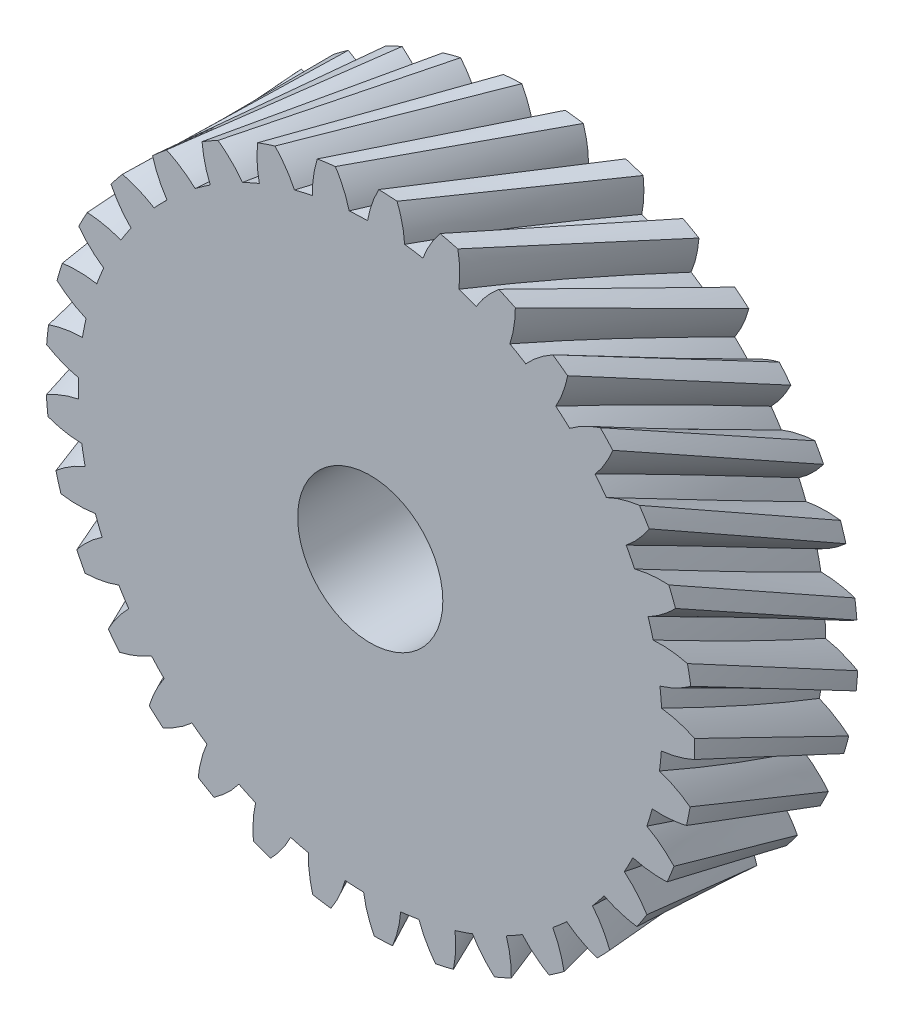
SolidWorks part; units mm, degrees
ref_plane "Front Plane" through (0, 0, 0) normal (0, 0, 1) x (1, 0, 0)
ref_plane "Top Plane" through (0, 0, 0) normal (0, 1, 0) x (1, 0, 0)
ref_plane "Right Plane" through (0, 0, 0) normal (1, 0, 0) x (0, 0, -1)
sketch "Sketch1" plane through (0, 0, 0) normal (0, 0, 1) x (1, 0, 0)
  line L0 (0, 0) -> (0, 23.975) construction
  line L1 (0, 0) -> (-5.1891, 23.4067) construction
  line L2 (0, 0) -> (-10.1323, 21.7287) construction
  line L3 (0, 0) -> (-14.5951, 19.0206) construction
  line L4 (0, 0) -> (-18.3659, 15.4108) construction
  line L5 (-5.1891, 23.4067) -> (-0.0831, 24.5387) construction
  line L6 (-10.1323, 21.7287) -> (-0.6523, 26.1493) construction
  line L7 (-14.5951, 19.0206) -> (-2.1473, 28.5721) construction
  line L8 (-18.3659, 15.4108) -> (-4.9188, 31.4365) construction
  line L9 (-0.4327, 25.6163) -> (-2.8676, 25.459) construction
  line L10 (-1.6502, 25.5377) -> (0, 0) construction
  circle A0 centre (0, 0) radius 23.975 construction
  circle A1 centre (0, 0) radius 25.62 construction
  arc A2 (-0.9749, 26.8023) -> (-2.4825, 26.7049) centre (0, 0) ccw
  circle A3 centre (0, 0) radius 24.12
  spline S0 degree 3 poles (-0.0236, 24.12) (-0.146, 24.8291) (-0.4377, 25.7372) (-0.8595, 26.5883) (-0.9749, 26.8023) knots 0.015866 0.015866 0.015866 0.015866 0.249383 0.329607 0.329607 0.329607 0.329607
  spline S1 degree 3 poles (-3.0807, 23.9224) (-3.0507, 24.6414) (-2.8782, 25.5795) (-2.5695, 26.4778) (-2.4825, 26.7049) knots 0.015866 0.015866 0.015866 0.015866 0.249383 0.329607 0.329607 0.329607 0.329607
  point P11 (0, 0)
  dimension "D3" = 47.95
  dimension "D8" = 51.24
  dimension "D10" = 53.64
  dimension "D11" = 48.24
  dimension "D2" = 50
  dimension "D4" = 5.23
  dimension "D5" = 10.46
  dimension "D6" = 15.69
  dimension "D7" = 20.92
  dimension "D9" = 2.44
  dimension "D1" = 5
sketch "Sketch2" plane through (0, 0, 0) normal (0, 0, 1) x (1, 0, 0)
  circle A0 centre (0, 0) radius 24.12
  dimension "D1" = 48.24
extrude "Boss-Extrude1" add sketch "Sketch2" along normal blind 13.5
sketch "Sketch3" plane through (0, 0, 13.5) normal (0, 0, 1) x (1, 0, 0)
  arc A2 (-6.2655, 23.292) -> (-9.1673, 22.31) centre (0, 0) ccw
  arc A3 (-7.8787, 25.6367) -> (-9.3097, 25.1524) centre (0, 0) ccw
  spline S2 degree 3 poles (-6.2655, 23.292) (-6.5672, 23.9453) (-7.0841, 24.7469) (-7.7118, 25.4599) (-7.8787, 25.6367) knots 0.015866 0.015866 0.015866 0.015866 0.249383 0.329607 0.329607 0.329607 0.329607
  spline S3 degree 3 poles (-9.1673, 22.31) (-9.3244, 23.0122) (-9.4006, 23.963) (-9.3349, 24.9106) (-9.3097, 25.1524) knots 0.015866 0.015866 0.015866 0.015866 0.249383 0.329607 0.329607 0.329607 0.329607
sketch "Sketch4" plane through (0, 0, 0) normal (0, 0, -1) x (-1, 0, 0)
  circle A0 centre (0, 0) radius 24.12 construction
  arc A1 (2.4825, 26.7049) -> (0.9749, 26.8023) centre (0, 0) ccw construction
  arc A2 (3.0807, 23.9224) -> (0.0236, 24.12) centre (0, 0) ccw
  arc A3 (2.4825, 26.7049) -> (0.9749, 26.8023) centre (0, 0) ccw
  spline S0 degree 3 poles (-1992.9931, -75.3017) (-110.5887, -68.1723) (152.4248, 74.6075) (-192.129, 40.0055) (1991.5783, -181.0819) knots -9.448528 -9.448528 -9.448528 -9.448528 0.249383 11.497593 11.497593 11.497593 11.497593 only from (3.0807, 23.9224) to (2.4825, 26.7049) construction
  spline S1 degree 3 poles (1966.7302, -331.1579) (100.8954, -81.8376) (-141.5553, 93.6035) (195.6796, 14.9466) (-1998.3252, 76.7205) knots -9.448521 -9.448521 -9.448521 -9.448521 0.249383 11.497584 11.497584 11.497584 11.497584 only from (0.0236, 24.12) to (0.9749, 26.8023) construction
  spline S2 degree 3 poles (3.0807, 23.9224) (3.0507, 24.6414) (2.8782, 25.5795) (2.5695, 26.4778) (2.4825, 26.7049) knots 0.015866 0.015866 0.015866 0.015866 0.249383 0.329607 0.329607 0.329607 0.329607
  spline S3 degree 3 poles (0.0236, 24.12) (0.146, 24.8291) (0.4377, 25.7372) (0.8595, 26.5883) (0.9749, 26.8023) knots 0.015866 0.015866 0.015866 0.015866 0.249383 0.329607 0.329607 0.329607 0.329607
loft "Loft1" add profiles "Sketch4", "Sketch3"
pattern_circular "CirPattern1" count 33 over 360 of "Loft1"
sketch "Sketch5" plane through (0, 0, 0) normal (0, 0, -1) x (-1, 0, 0)
  circle A0 centre (0, 0) radius 6
  dimension "D1" = 12
extrude "Cut-Extrude1" cut sketch "Sketch5" against normal through all
sketch "Sketch6" plane through (0, 0, 0) normal (0, 0, -1) x (-1, 0, 0)
  line L0 (0, 0) -> (0, 6) construction
  line L1 (-3, 5.1962) -> (3, 5.1962)
  line L2 (-3, 5.1962) -> (-3, 6.9962)
  line L3 (-3, 6.9962) -> (3, 6.9962)
  line L4 (3, 5.1962) -> (3, 6.9962)
  circle A0 centre (0, 0) radius 6 construction
  point P9 (-2.1707, 5.5936)
  dimension "D1" = 1.8
  dimension "D2" = 6
extrude "Cut-Extrude2" cut sketch "Sketch6" against normal blind 6
